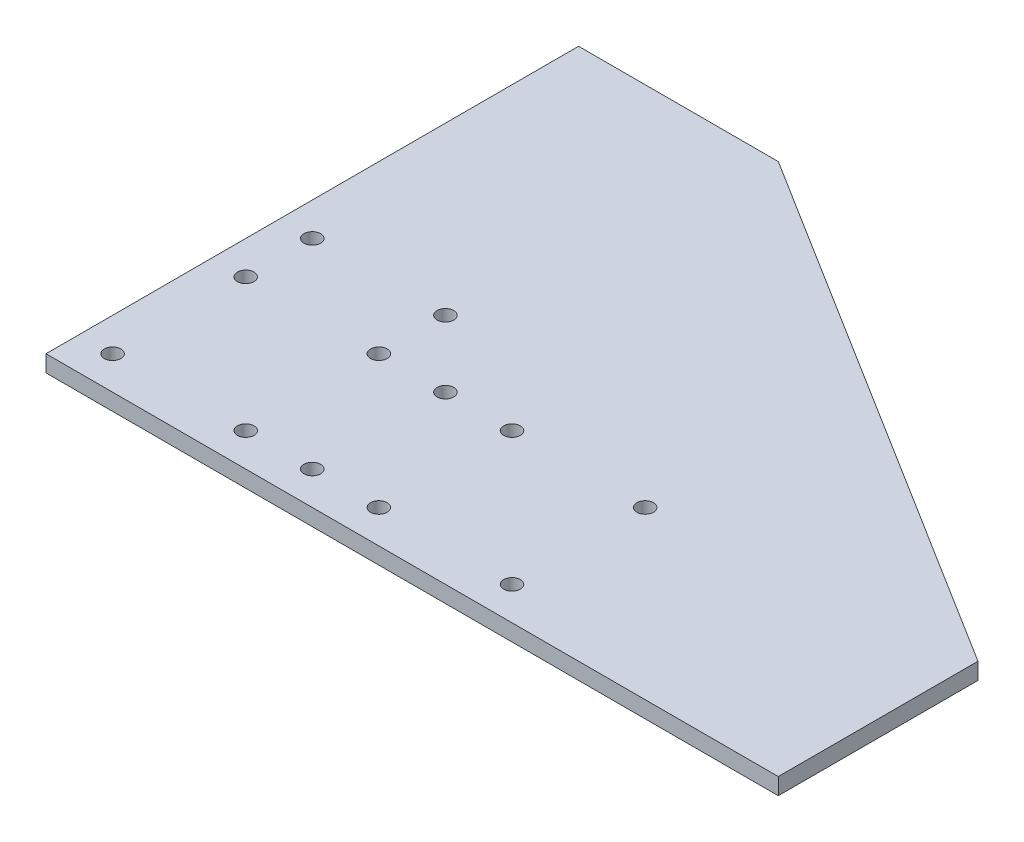
SolidWorks part; units mm, degrees
ref_plane "Front Plane" through (0, 0, 0) normal (0, 0, 1) x (1, 0, 0)
ref_plane "Top Plane" through (0, 0, 0) normal (0, 1, 0) x (1, 0, 0)
ref_plane "Right Plane" through (0, 0, 0) normal (1, 0, 0) x (0, 0, -1)
sketch "Sketch1" plane through (0, 0, 0) normal (0, 1, 0) x (1, 0, 0)
  line L0 (0, 50.8) -> (0, 0)
  line L1 (0, 0) -> (88.9, 0)
  line L2 (88.9, 0) -> (88.9, 38.1)
  line L3 (88.9, 38.1) -> (38.1, 38.1)
  line L4 (38.1, 38.1) -> (38.1, 50.8)
  line L5 (38.1, 50.8) -> (0, 50.8)
  dimension "D1" = 38.1
  dimension "D2" = 38.1
  dimension "D3" = 88.9
  dimension "D4" = 50.8
extrude "Boss-Extrude1" add sketch "Sketch1" along normal blind 3.175
sketch "Sketch2" plane through (0, 3.175, 0) normal (0, 1, 0) x (1, 0, 0)
  line L0 (88.9, 38.1) -> (38.1, 38.1) construction
  line L1 (6.35, 44.45) -> (31.75, 44.45) construction
  line L2 (6.35, 44.45) -> (6.35, 6.35) construction
  line L3 (6.35, 6.35) -> (31.75, 6.35) construction
  line L4 (31.75, 44.45) -> (31.75, 6.35) construction
  line L5 (6.35, 6.35) -> (82.55, 6.35) construction
  line L6 (6.35, 6.35) -> (6.35, 31.75) construction
  line L7 (6.35, 31.75) -> (82.55, 31.75) construction
  line L8 (82.55, 6.35) -> (82.55, 31.75) construction
  line L9 (38.1, 38.1) -> (38.1, 50.8) construction
  line L10 (38.1, 50.8) -> (0, 50.8) construction
  line L11 (6.35, 31.75) -> (31.75, 6.35) construction
  line L12 (31.75, 6.35) -> (57.15, 31.75) construction
  line L13 (57.15, 31.75) -> (82.55, 6.35) construction
  line L14 (88.9, 0) -> (88.9, 38.1) construction
  line L15 (38.1, 38.1) -> (38.1, 0) construction
  line L16 (0, 0) -> (88.9, 0) construction
  line L17 (44.45, 38.1) -> (44.45, -0.0007) construction
  line L18 (57.15, 31.75) -> (57.15, 6.35) construction
  circle A0 centre (6.35, 44.45) radius 1.5875
  circle A1 centre (31.75, 44.45) radius 1.5875
  circle A2 centre (31.75, 31.75) radius 1.5875
  circle A3 centre (6.35, 31.75) radius 1.5875
  circle A4 centre (6.35, 6.35) radius 1.5875
  circle A5 centre (31.75, 6.35) radius 1.5875
  circle A6 centre (82.55, 6.35) radius 1.5875
  circle A7 centre (82.55, 31.75) radius 1.5875
  circle A8 centre (57.15, 31.75) radius 1.5875
  circle A9 centre (57.15, 6.35) radius 1.5875
  circle A10 centre (44.45, 6.35) radius 1.5875
  circle A11 centre (44.45, 31.75) radius 1.5875
  dimension "D9" = 3.175
  dimension "D1" = 25.4
  dimension "D2" = 25.4
  dimension "D3" = 6.35
  dimension "D4" = 6.35
  dimension "D5" = 6.35
  dimension "D6" = 25.4
  dimension "D7" = 6.35
  dimension "D8" = 6.35
extrude "Cut-Extrude1" cut sketch "Sketch2" against normal through all
sketch "Sketch3" plane through (0, 3.175, 0) normal (0, 1, 0) x (1, 0, 0)
  line L1 (0, 101.6) -> (38.1, 101.6)
  line L2 (38.1, 101.6) -> (139.7, 38.1)
  line L3 (139.7, 38.1) -> (139.7, 0)
  line L4 (139.7, 0) -> (0, 0) construction
  line L6 (0, 50.8) -> (38.1, 50.8)
  line L7 (38.1, 50.8) -> (38.1, 38.1)
  line L8 (38.1, 38.1) -> (88.9, 38.1)
  line L9 (88.9, 38.1) -> (88.9, 0)
  line L10 (88.9, 0) -> (139.7, 0)
  line L11 (0, 50.8) -> (0, 0) construction
  line L12 (0, 101.6) -> (0, 50.8)
  dimension "D1" = 50.8
  dimension "D2" = 50.8
  dimension "D3" = 38.1
  dimension "D4" = 38.1
extrude "Boss-Extrude2" add sketch "Sketch3" against normal up to surface (3.175 mm away) up to face at (57.15, 0, -30.1625)
